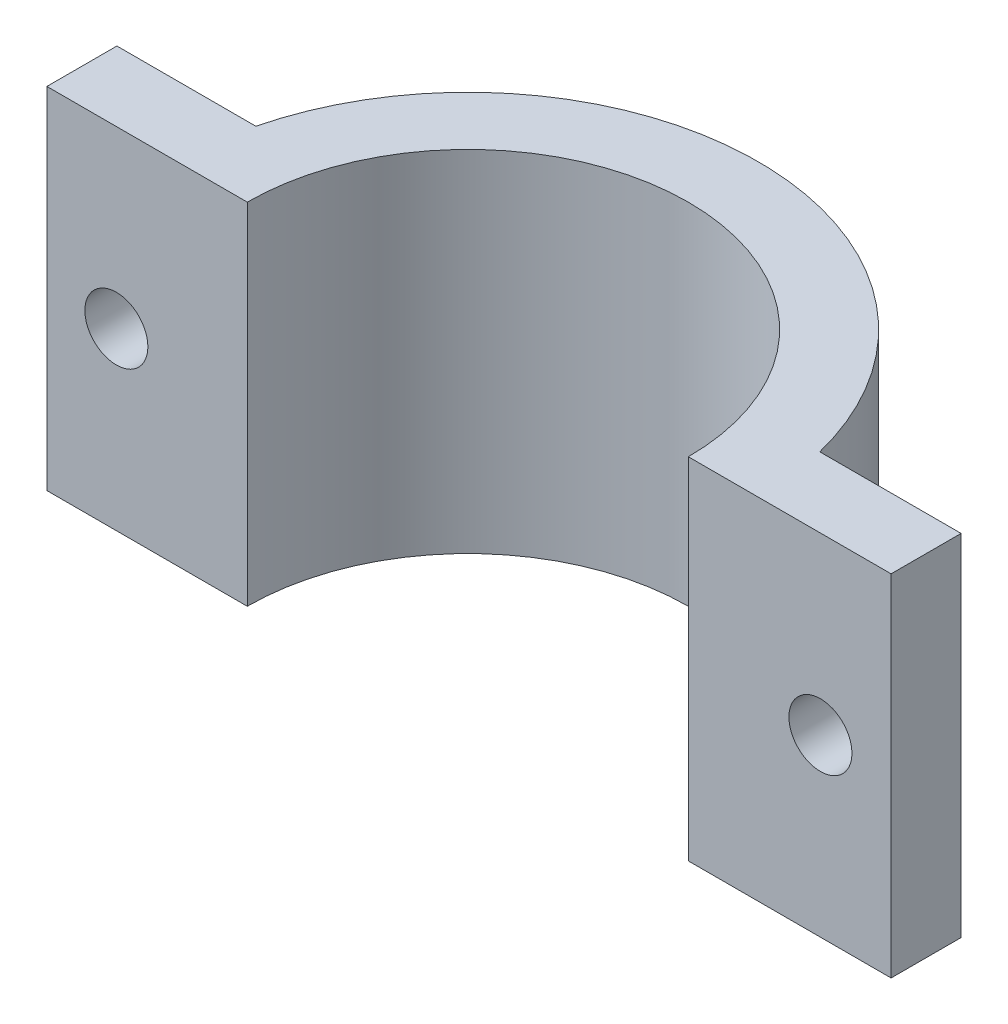
SolidWorks part; units mm, degrees
ref_plane "Front Plane" through (0, 0, 0) normal (0, 0, 1) x (1, 0, 0)
ref_plane "Top Plane" through (0, 0, 0) normal (0, 1, 0) x (1, 0, 0)
ref_plane "Right Plane" through (0, 0, 0) normal (1, 0, 0) x (0, 0, -1)
sketch "Sketch1" plane through (0, 0, 0) normal (0, 1, 0) x (1, 0, 0)
  line L0 (-26.035, 0) -> (-16.002, 0)
  line L5 (0, 0) -> (0, 50000) construction
  line L6 (16.002, 0) -> (26.035, 0)
  line L7 (20.4608, 5.08) -> (26.035, 5.08)
  line L8 (-26.035, 5.08) -> (-20.4608, 5.08)
  line L9 (-26.035, 5.08) -> (-30.5431, 5.08)
  line L10 (-30.5431, 5.08) -> (-30.5431, 0)
  line L11 (-30.5431, 0) -> (-26.035, 0)
  line L12 (26.035, 5.08) -> (30.7167, 5.08)
  line L13 (30.7167, 5.08) -> (30.7167, 0)
  line L14 (30.7167, 0) -> (26.035, 0)
  arc A0 (16.002, 0) -> (-16.002, 0) centre (0, 0) ccw
  arc A1 (20.4608, 5.08) -> (-20.4608, 5.08) centre (0, 0) ccw
  dimension "D2" = 5.08
  dimension "D4" = 16.002
  dimension "D1" = 52.07
extrude "Boss-Extrude1" add sketch "Sketch1" along normal blind 25.4
sketch "Sketch2" plane through (0, 0, -5.08) normal (0, 0, -1) x (-1, 0, 0)
  line L0 (-25.5887, 19.05) -> (-25.5887, -49980.95) construction
  line L1 (-30.7167, 25.4) -> (-20.4608, 25.4) construction
  line L3 (-30.7167, 12.7) -> (49969.2833, 12.7) construction
  line L4 (-30.7167, 25.4) -> (-30.7167, 0) construction
  circle A0 centre (-25.5887, 12.7) radius 2.286
  circle A1 centre (25.5019, 12.7) radius 2.286
  point P4 (-25.5887, 25.4)
  point P9 (-30.7167, 12.7)
  point P12 (25.5019, 12.7)
  dimension "D1" = 4.572
  dimension "D2" = 4.572
extrude "Cut-Extrude1" cut sketch "Sketch2" against normal through all
